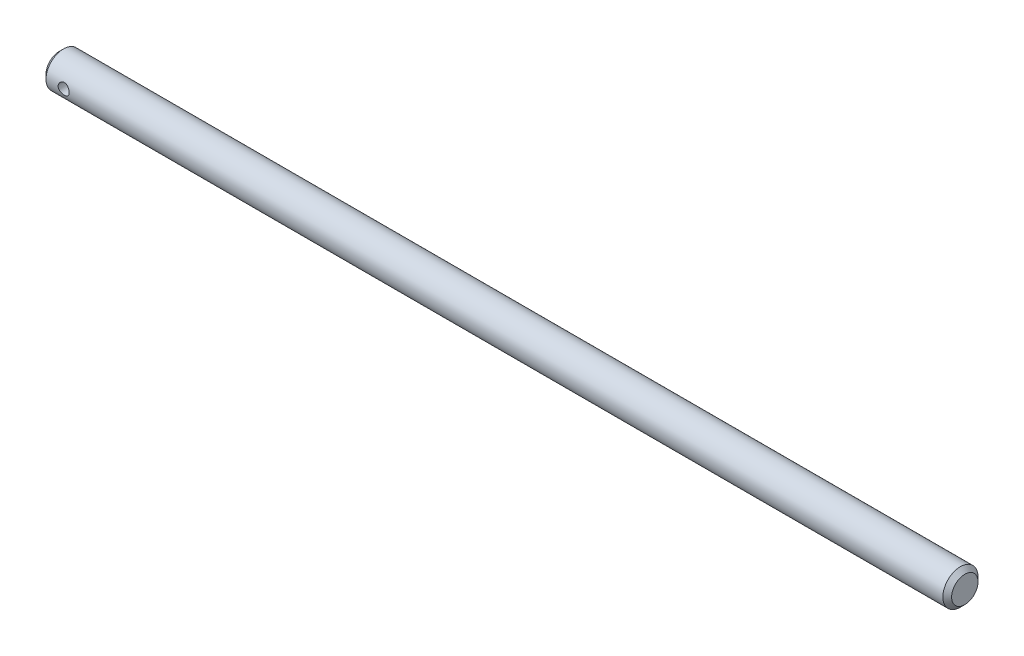
SolidWorks part; units mm, degrees
material "Plain Carbon Steel"
ref_plane "Front" through (0, 0, 0) normal (0, 0, 1) x (1, 0, 0)
ref_plane "Top" through (0, 0, 0) normal (0, 1, 0) x (1, 0, 0)
ref_plane "Right" through (0, 0, 0) normal (1, 0, 0) x (0, 0, -1)
sketch "Sketch1" plane through (0, 0, 0) normal (1, 0, 0) x (0, 0, -1)
  circle A0 centre (0, 0) radius 6.35
  dimension "D1" = 12.7
extrude "Boss-Extrude1" add sketch "Sketch1" along normal mid plane 327.025
chamfer "Chamfer1" distance 1.5875 angle 45
sketch "Sketch2" plane through (0, 0, 0) normal (0, 0, 1) x (1, 0, 0)
  line L0 (-161.925, 6.35) -> (-161.925, -6.35) construction
  line L1 (-161.925, 6.35) -> (-161.925, -6.35) construction
  circle A0 centre (-155.575, 0) radius 1.9844
  point P5 (-161.925, 0)
  dimension "D1" = 3.9688
  dimension "D2" = 6.35
extrude "Cut-Extrude1" cut sketch "Sketch2" against normal through all both and the other way through all contours A0
equation "\"Total Cutting Length\"= \"Cutting Length-Outer\" + \"Cutting Length-Inner\""
equation "\"Amount in ft^2\"= \"Bounding Box Area-Blank\" / 144"
